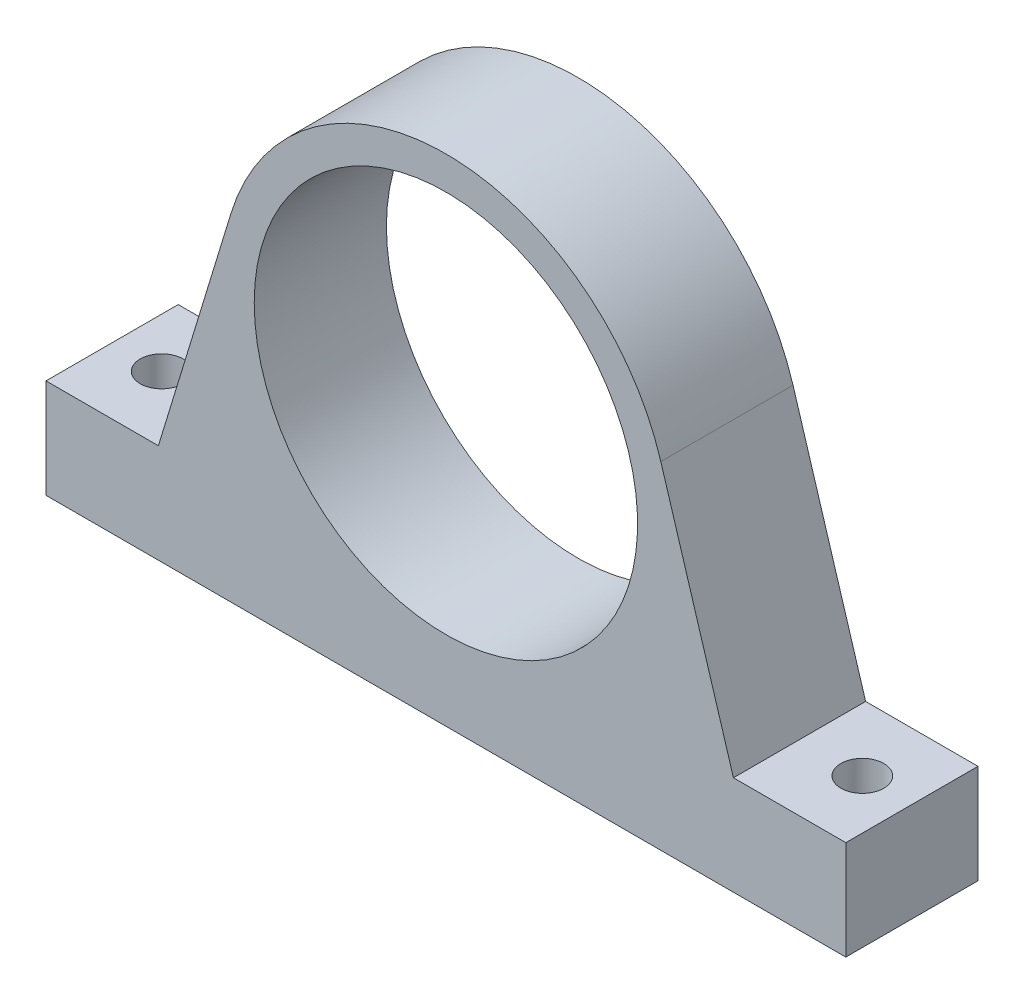
SolidWorks part; units mm, degrees
other "Markup1"
sketch "Sketch4" plane through (-60.5, 75, 0) normal (-0.0501, 0.3067, -0.9505) x (-0.9986, 0.0018, 0.0533)
material "Nylon 101"
ref_plane "X-Y Datum" through (0, 0, 0) normal (0, 0, 1) x (1, 0, 0)
ref_plane "X-Z Datum" through (0, 0, 0) normal (0, 1, 0) x (1, 0, 0)
ref_plane "Y-Z Datum" through (0, 0, 0) normal (1, 0, 0) x (0, 0, -1)
sketch "Sketch1" plane through (0, 0, 0) normal (0, 0, 1) x (1, 0, 0)
  line L0 (-60.5, 0) -> (60.5, 0)
  line L1 (-60.5, 75) -> (52.1961, 75) construction
  line L2 (-60.5, 0) -> (-60.5, 15)
  line L3 (-60.5, 15) -> (-43.5, 15)
  line L4 (60.5, 15) -> (43.5, 15)
  line L5 (60.5, 0) -> (60.5, 15)
  line L8 (-43.5, 15) -> (-32.515, 50.9386)
  line L9 (43.5, 15) -> (32.515, 50.9386)
  arc A0 (-32.515, 50.9386) -> (32.515, 50.9386) centre (0, 41) cw
  point P3 (0, 0)
  dimension "D6" = 34
  dimension "D1" = 121
  dimension "D2" = 75
  dimension "D3" = 15
  dimension "D4" = 17
  dimension "D5" = 17
extrude "Boss-Extrude1" add sketch "Sketch1" along normal blind 20 contours A0 L9 L4 L5 L0 L2 L3 L8
sketch "Sketch2" plane through (0, 0, 0) normal (0, 0, -1) x (-1, 0, 0)
  circle A0 centre (0, 41) radius 29
  arc A1 (32.515, 50.9386) -> (-32.515, 50.9386) centre (0, 41) ccw construction
  dimension "D1" = 58
  dimension "D2" = 0
extrude "Cut-Extrude1" cut sketch "Sketch2" against normal through all both and the other way through all
sketch "Sketch3" plane through (0, 15, 0) normal (0, 1, 0) x (1, 0, 0)
  line L0 (-60.5, -20) -> (-60.5, 0) construction
  circle A0 centre (-53, -10) radius 3.25
  point P5 (-60.5, -10)
  dimension "D1" = 6.5
  dimension "D2" = 7.5
extrude "Cut-Extrude2" cut sketch "Sketch3" against normal through all both and the other way through all
mirror "Mirror1" about plane through (0, 0, 0) normal (1, 0, 0) of "Cut-Extrude2"
